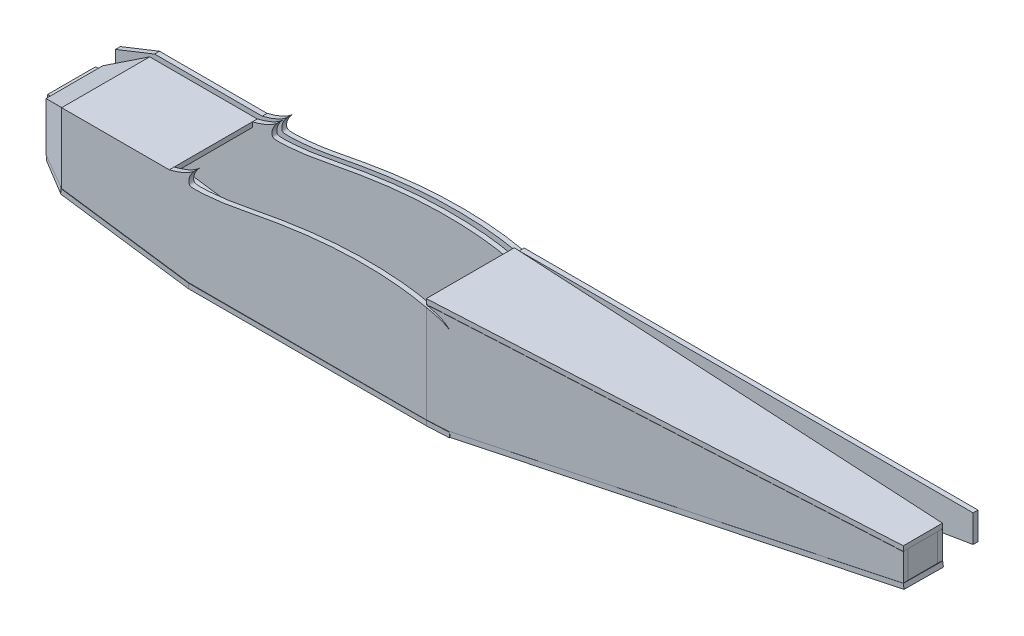
SolidWorks part; units mm, degrees
material "Default"
ref_plane "Front Plane" through (0, 0, 0) normal (0, 0, 1) x (1, 0, 0)
ref_plane "Top Plane" through (0, 0, 0) normal (0, 1, 0) x (1, 0, 0)
ref_plane "Right Plane" through (0, 0, 0) normal (1, 0, 0) x (0, 0, -1)
other "Center of Mass"
curve "Curve1"
  spline degree 3 poles (264.9706, 0.6908, 0) (266.2411, -0.1717, 0) (265.1272, 0.6583, 0) (264.3876, 1.3839, 0) (262.7456, 2.8995, 0) (260.8083, 4.5118, 0) (258.1583, 6.1371, 0) (254.863, 7.7123, 0) (250.8848, 9.3562, 0) (246.2298, 11.0459, 0) (240.9197, 12.7694, 0) (234.982, 14.5119, 0) (228.45, 16.2652, 0) (221.3598, 18.0131, 0) (213.752, 19.7429, 0) (205.6719, 21.444, 0) (197.169, 23.1075, 0) (188.2928, 24.713, 0) (179.0993, 26.2581, 0) (169.6415, 27.723, 0) (159.9806, 29.1106, 0) (150.1784, 30.4098, 0) (140.3059, 31.6165, 0) (130.4421, 32.7392, 0) (120.6687, 33.7497, 0) (111.0652, 34.6289, 0) (101.6992, 35.3274, 0) (92.6242, 35.8079, 0) (83.8906, 36.0154, 0) (75.5433, 35.9933, 0) (67.5978, 35.5846, 0) (60.0511, 34.7564, 0) (52.8723, 33.5853, 0) (46.0598, 32.0681, 0) (39.6205, 30.289, 0) (33.5818, 28.2794, 0) (27.9692, 26.0865, 0) (22.8177, 23.7219, 0) (18.1438, 21.2336, 0) (13.9729, 18.6499, 0) (10.3312, 16.0059, 0) (7.2202, 13.3576, 0) (4.6849, 10.676, 0) (2.7376, 7.9845, 0) (1.2991, 5.366, 0) (0.3772, 2.8798, 0) (-0.0621, 0.5851, 0) (0.0227, -1.3557, 0) (0.5223, -3.1357, 0) (2.3797, -4.0193, 0) (4.8769, -4.1433, 0) (8.293, -4.2635, 0) (12.5891, -4.0782, 0) (17.7166, -3.7378, 0) (23.6183, -3.1924, 0) (30.2339, -2.4546, 0) (37.5312, -1.5084, 0) (45.5065, -0.186, 0) (54.1987, 1.4724, 0) (63.6513, 3.2771, 0) (73.8181, 5.1827, 0) (84.6351, 7.11, 0) (96.023, 8.9867, 0) (107.8934, 10.7501, 0) (120.1441, 12.3356, 0) (132.6647, 13.6969, 0) (145.3372, 14.7729, 0) (158.0342, 15.5357, 0) (170.6232, 15.9551, 0) (182.9675, 16.008, 0) (194.9296, 15.691, 0) (206.3723, 15.0115, 0) (217.1581, 13.9781, 0) (227.1585, 12.6306, 0) (236.2435, 11.0081, 0) (244.3064, 9.1649, 0) (251.1986, 7.1926, 0) (256.8393, 5.0876, 0) (260.8637, 3.1612, 0) (263.8308, 1.3801, 0) (264.9706, 0.6908, 0) (266.2411, -0.1717, 0) (265.1272, 0.6583, 0) knots -0.009748 -0.004147 -0.001 0 0.00098 0.003649 0.007483 0.012095 0.017526 0.024052 0.031783 0.040678 0.05071 0.061833 0.073989 0.087118 0.101145 0.115991 0.13157 0.147788 0.164551 0.181758 0.199312 0.217095 0.23499 0.252857 0.270541 0.287887 0.304773 0.321101 0.336806 0.3518 0.366031 0.379616 0.392653 0.40517 0.417172 0.428604 0.439419 0.449597 0.459102 0.467908 0.475988 0.483309 0.489875 0.495803 0.501149 0.505903 0.510047 0.513579 0.516447 0.51935 0.523823 0.529974 0.537716 0.546968 0.557637 0.56962 0.582804 0.597247 0.613135 0.630444 0.649056 0.668822 0.689595 0.71119 0.733427 0.756094 0.778989 0.80189 0.824567 0.846792 0.868338 0.888978 0.908492 0.926659 0.943286 0.958169 0.971136 0.981956 0.990252 0.995853 0.999 1 1.00098 1.003649 1.007483 periodic
sketch "Sketch2" plane through (0, 0, 0) normal (0, 0, 1) x (1, 0, 0)
  line L0 (242.745, 12.1672) -> (706.745, 12.1672)
  line L1 (706.745, 12.1672) -> (706.745, -15.8895)
  line L3 (0, 0) -> (-0.0046, 0)
  line L4 (-130, 0) -> (-20, 0)
  line L5 (-20, 0) -> (-130, 0)
  line L6 (124.4328, 12.1672) -> (124.4328, 12.7877)
  line L7 (-0.0046, 0) -> (-0.0046, -0.1771)
  line L8 (265.9954, -90) -> (706.745, -15.8895)
  line L13 (124.4328, 12.1672) -> (119.0969, 12.1672) construction
  line L14 (-0.0046, -90) -> (265.9954, -90)
  line L16 (-170, -15.8895) -> (-170, -65.8895) construction
  line L17 (-130, 0) -> (-170, -15.8895)
  line L18 (-170, -15.8895) -> (-170, -65.8895)
  line L19 (-170, -65.8895) -> (-0.0046, -90)
  spline S0 degree 3 poles (264.9706, 0.6908) (266.2411, -0.1717) (265.1272, 0.6583) (264.3876, 1.3839) (262.7456, 2.8995) (260.8083, 4.5118) (258.1583, 6.1371) (254.863, 7.7123) (250.8848, 9.3562) (246.2298, 11.0459) (240.9197, 12.7694) (234.982, 14.5119) (228.45, 16.2652) (221.3598, 18.0131) (213.752, 19.7429) (205.6719, 21.444) (197.169, 23.1075) (188.2928, 24.713) (179.0993, 26.2581) (169.6415, 27.723) (159.9806, 29.1106) (150.1784, 30.4098) (140.3059, 31.6165) (130.4421, 32.7392) (120.6687, 33.7497) (111.0652, 34.6289) (101.6992, 35.3274) (92.6242, 35.8079) (83.8906, 36.0154) (75.5433, 35.9933) (67.5978, 35.5846) (60.0511, 34.7564) (52.8723, 33.5853) (46.0598, 32.0681) (39.6205, 30.289) (33.5818, 28.2794) (27.9692, 26.0865) (22.8177, 23.7219) (18.1438, 21.2336) (13.9729, 18.6499) (10.3312, 16.0059) (7.2202, 13.3576) (4.6849, 10.676) (2.7376, 7.9845) (1.2991, 5.366) (0.3772, 2.8798) (-0.0621, 0.5851) (0.0227, -1.3557) (0.5223, -3.1357) (2.3797, -4.0193) (4.8769, -4.1433) (8.293, -4.2635) (12.5891, -4.0782) (17.7166, -3.7378) (23.6183, -3.1924) (30.2339, -2.4546) (37.5312, -1.5084) (45.5065, -0.186) (54.1987, 1.4724) (63.6513, 3.2771) (73.8181, 5.1827) (84.6351, 7.11) (96.023, 8.9867) (107.8934, 10.7501) (120.1441, 12.3356) (132.6647, 13.6969) (145.3372, 14.7729) (158.0342, 15.5357) (170.6232, 15.9551) (182.9675, 16.008) (194.9296, 15.691) (206.3723, 15.0115) (217.1581, 13.9781) (227.1585, 12.6306) (236.2435, 11.0081) (244.3064, 9.1649) (251.1986, 7.1926) (256.8393, 5.0876) (260.8637, 3.1612) (263.8308, 1.3801) (264.9706, 0.6908) (266.2411, -0.1717) (265.1272, 0.6583) knots -0.009748 -0.004147 -0.001 0 0.00098 0.003649 0.007483 0.012095 0.017526 0.024052 0.031783 0.040678 0.05071 0.061833 0.073989 0.087118 0.101145 0.115991 0.13157 0.147788 0.164551 0.181758 0.199312 0.217095 0.23499 0.252857 0.270541 0.287887 0.304773 0.321101 0.336806 0.3518 0.366031 0.379616 0.392653 0.40517 0.417172 0.428604 0.439419 0.449597 0.459102 0.467908 0.475988 0.483309 0.489875 0.495803 0.501149 0.505903 0.510047 0.513579 0.516447 0.51935 0.523823 0.529974 0.537716 0.546968 0.557637 0.56962 0.582804 0.597247 0.613135 0.630444 0.649056 0.668822 0.689595 0.71119 0.733427 0.756094 0.778989 0.80189 0.824567 0.846792 0.868338 0.888978 0.908492 0.926659 0.943286 0.958169 0.971136 0.981956 0.990252 0.995853 0.999 1 1.00098 1.003649 1.007483 only from (266, 0) to (266, 0) construction
  spline S1 degree 3 poles (7.0158, 13.0653) (6.1882, 12.2656) (4.6442, 10.6197) (2.7376, 7.9845) (1.2991, 5.366) (0.3772, 2.8798) (-0.0621, 0.5851) (0.0227, -1.3557) (0.5223, -3.1357) (2.3797, -4.0193) (4.8769, -4.1433) (8.293, -4.2635) (12.5891, -4.0782) (17.7166, -3.7378) (23.6183, -3.1924) (30.2339, -2.4546) (37.5312, -1.5084) (45.5065, -0.186) (54.1987, 1.4724) (63.6513, 3.2771) (73.8181, 5.1827) (84.6351, 7.11) (96.023, 8.9867) (107.8934, 10.7501) (120.1441, 12.3356) (132.6647, 13.6969) (145.3372, 14.7729) (158.0342, 15.5357) (170.6232, 15.9551) (182.9675, 16.008) (194.9296, 15.691) (206.3723, 15.0115) (217.1581, 13.9781) (227.1585, 12.6306) (236.2435, 11.0081) (244.3064, 9.1649) (251.1986, 7.1926) (256.8393, 5.0876) (260.8637, 3.1612) (263.8308, 1.3801) (264.9706, 0.6908) (266.2411, -0.1717) (265.1272, 0.6583) (264.3876, 1.3839) (262.7456, 2.8995) (260.8083, 4.5118) (258.1583, 6.1371) (254.863, 7.7123) (250.8848, 9.3562) (246.7685, 10.8503) (243.9744, 11.7746) (242.745, 12.1672) knots 0.483683 0.483683 0.483683 0.483683 0.489875 0.495803 0.501149 0.505903 0.510047 0.513579 0.516447 0.51935 0.523823 0.529974 0.537716 0.546968 0.557637 0.56962 0.582804 0.597247 0.613135 0.630444 0.649056 0.668822 0.689595 0.71119 0.733427 0.756094 0.778989 0.80189 0.824567 0.846792 0.868338 0.888978 0.908492 0.926659 0.943286 0.958169 0.971136 0.981956 0.990252 0.995853 0.999 1 1.00098 1.003649 1.007483 1.012095 1.017526 1.024052 1.031783 1.040678 1.047625 1.047625 1.047625 1.047625
  spline S2 degree 3 poles (-20, 0) (-11.0921, 2.2966) (0.1137, 5.807) (7.0158, 13.0653) knots 0 0 0 0 0.787091 0.787091 0.787091 0.787091
  dimension "D1" = 464
  dimension "D2" = 130
  dimension "D5" = 28.0567
extrude "Boss-Extrude1" add sketch "Sketch2" along normal blind 5
ref_plane "Plane2" through (0, 0, 100) normal (0, 0, 1) x (1, 0, 0)
sketch "Sketch7" plane through (0, 0, 100) normal (0, 0, 1) x (1, 0, 0)
  line L0 (242.745, 12.1672) -> (242.745, -90)
  line L1 (242.745, -90) -> (265.9954, -90)
  line L2 (-130, 0) -> (-130, -71.5627)
  line L3 (242.745, 9.4844) -> (242.745, 8.9727)
  line L4 (-130, 0) -> (-130, -71.5627)
  line L5 (242.745, 8.9727) -> (242.745, 9.4844)
  line L6 (-130, 0) -> (-130, -71.5627)
  line L7 (242.745, 9.4844) -> (242.745, -90)
  line L8 (-20, 0) -> (-130, 0)
  line L9 (-130, 0) -> (-170, -15.8895)
  line L10 (-170, -15.8895) -> (-170, -65.8895)
  line L11 (-170, -65.8895) -> (-0.0046, -90)
  line L12 (-0.0046, -90) -> (265.9954, -90)
  line L13 (265.9954, -90) -> (706.745, -15.8895)
  line L14 (706.745, -15.8895) -> (706.745, 12.1672)
  line L15 (706.745, 12.1672) -> (242.745, 12.1672)
  line L16 (-20, 0) -> (-130, 0)
  line L17 (-130, 0) -> (-170, -15.8895)
  line L18 (-170, -15.8895) -> (-170, -65.8895)
  line L19 (-170, -65.8895) -> (-0.0046, -90)
  line L20 (-0.0046, -90) -> (265.9954, -90)
  line L21 (265.9954, -90) -> (706.745, -15.8895)
  line L22 (706.745, -15.8895) -> (706.745, 12.1672)
  line L23 (706.745, 12.1672) -> (242.745, 12.1672)
  spline S0 degree 3 poles (242.745, 9.4844) (240.69, 9.9881) (235.6053, 11.1221) (227.1585, 12.6306) (217.1581, 13.9781) (206.3723, 15.0115) (194.9296, 15.691) (182.9675, 16.008) (170.6232, 15.9551) (158.0342, 15.5357) (145.3372, 14.7729) (132.6647, 13.6969) (120.1441, 12.3356) (107.8934, 10.7501) (96.023, 8.9867) (84.6351, 7.11) (73.8181, 5.1827) (63.6513, 3.2771) (54.1987, 1.4724) (45.5065, -0.186) (37.5312, -1.5084) (30.2339, -2.4546) (23.6183, -3.1924) (17.7166, -3.7378) (12.5891, -4.0782) (8.293, -4.2635) (4.8769, -4.1433) (2.3797, -4.0193) (0.5223, -3.1357) (0.0227, -1.3557) (-0.0621, 0.5851) (0.3772, 2.8798) (1.2991, 5.366) (2.7376, 7.9845) (4.3959, 10.2766) (5.6165, 11.6415) (6.1205, 12.1672) knots 0.578902 0.578902 0.578902 0.578902 0.590296 0.606923 0.62509 0.644604 0.665244 0.68679 0.709016 0.731692 0.754594 0.777488 0.800155 0.822393 0.843987 0.86476 0.884526 0.903139 0.920447 0.936335 0.950778 0.963962 0.975945 0.986614 0.995867 1.003608 1.009759 1.014232 1.017135 1.020003 1.023535 1.027679 1.032433 1.037779 1.043708 1.047625 1.047625 1.047625 1.047625
  spline S2 degree 3 poles (2011.2676, 4666.7582) (-142.2329, -124.2279) (96.248, 65.4868) (250.8848, 9.3562) (254.863, 7.7123) (258.1583, 6.1371) (260.8083, 4.5118) (262.7456, 2.8995) (264.3876, 1.3839) (265.1272, 0.6583) (266.2411, -0.1717) (264.9706, 0.6908) (263.8308, 1.3801) (260.8637, 3.1612) (256.8393, 5.0876) (251.1986, 7.1926) (244.3064, 9.1649) (236.2435, 11.0081) (227.1585, 12.6306) (217.1581, 13.9781) (206.3723, 15.0115) (194.9296, 15.691) (182.9675, 16.008) (170.6232, 15.9551) (158.0342, 15.5357) (145.3372, 14.7729) (132.6647, 13.6969) (120.1441, 12.3356) (107.8934, 10.7501) (96.023, 8.9867) (84.6351, 7.11) (73.8181, 5.1827) (63.6513, 3.2771) (54.1987, 1.4724) (45.5065, -0.186) (37.5312, -1.5084) (30.2339, -2.4546) (23.6183, -3.1924) (17.7166, -3.7378) (12.5891, -4.0782) (8.293, -4.2635) (4.8769, -4.1433) (2.3797, -4.0193) (0.5223, -3.1357) (0.0227, -1.3557) (-0.0621, 0.5851) (0.3772, 2.8798) (1.2991, 5.366) (2.7376, 7.9845) (49.3907, 72.4654) (363.3472, -85.3871) (-4760.2536, 1520.3218) knots -0.376049 -0.376049 -0.376049 -0.376049 0.492904 0.501799 0.50953 0.516057 0.521487 0.526099 0.529933 0.532602 0.533582 0.534582 0.53773 0.54333 0.551627 0.562446 0.575413 0.590296 0.606923 0.62509 0.644604 0.665244 0.68679 0.709016 0.731692 0.754594 0.777488 0.800155 0.822393 0.843987 0.86476 0.884526 0.903139 0.920447 0.936335 0.950778 0.963962 0.975945 0.986614 0.995867 1.003608 1.009759 1.014232 1.017135 1.020003 1.023535 1.027679 1.032433 1.037779 1.043708 1.459832 1.459832 1.459832 1.459832 only from (242.745, 12.1672) to (6.1205, 12.1672)
  spline S3 degree 3 poles (-2585.8794, 1507.7799) (2947.8526, -1206.4866) (-3071.6527, 1002.673) (2847.1057, -882.3761) knots -5.429819 -5.429819 -5.429819 -5.429819 6.58664 6.58664 6.58664 6.58664 only from (6.1205, 12.1672) to (-20, 0)
  spline S4 degree 3 poles (242.745, 12.1672) (243.9744, 11.7746) (246.7685, 10.8503) (250.8848, 9.3562) (254.863, 7.7123) (258.1583, 6.1371) (260.8083, 4.5118) (262.7456, 2.8995) (264.3876, 1.3839) (265.1272, 0.6583) (266.2411, -0.1717) (264.9706, 0.6908) (263.8308, 1.3801) (260.8637, 3.1612) (256.8393, 5.0876) (251.1986, 7.1926) (246.3371, 8.5838) (243.3744, 9.3301) (242.745, 9.4844) knots 0.485957 0.485957 0.485957 0.485957 0.492904 0.501799 0.50953 0.516057 0.521487 0.526099 0.529933 0.532602 0.533582 0.534582 0.53773 0.54333 0.551627 0.562446 0.575413 0.578902 0.578902 0.578902 0.578902
  spline S5 degree 3 poles (6.1205, 12.1672) (-0.8269, 5.5132) (-11.4676, 2.1998) (-20, 0) knots 0 0 0 0 0.753912 0.753912 0.753912 0.753912
  dimension "D2" = 50
  dimension "D1" = 0
ref_plane "Plane3" through (6.088, 0, 112.7755) normal (0.0539, 0, 0.9985) x (0, -1, 0)
sketch "Sketch9" plane through (6.088, 0, 112.7755) normal (0.0539, 0, 0.9985) x (0, -1, 0)
sketch "Sketch12" plane through (6.088, 0, 112.7755) normal (0.0539, 0, 0.9985) x (0, -1, 0)
  line L0 (15.8895, 700.327) -> (-12.1672, 700.327) construction
  line L1 (90, 260.2182) -> (15.8895, 700.327) construction
  line L2 (90, 237.0016) -> (90, 260.2182) construction
  line L3 (-12.1672, 700.327) -> (-12.1672, 237.0016) construction
  line L4 (15.8895, 700.327) -> (-12.1672, 700.327)
  line L5 (90, 260.2182) -> (15.8895, 700.327)
  line L6 (90, 237.0016) -> (90, 260.2182)
  line L7 (-12.1672, 700.327) -> (-12.1672, 237.0016)
  line L8 (-9.5488, 236.7508) -> (-9.4844, 237.0016)
  line L9 (-9.4844, 237.0016) -> (90, 237.0016)
  spline S0 degree 3 poles (-1920.9953, 797.0816) (45.2116, -34.5204) (-51.6861, 128.6823) (-9.3562, 245.1296) (-7.7123, 249.102) (-6.1371, 252.3925) (-4.5118, 255.0387) (-2.8995, 256.9731) (-1.3839, 258.6128) (-0.6583, 259.3512) (0.1717, 260.4636) (-0.6908, 259.1949) (-1.3801, 258.0568) (-3.1612, 255.094) (-5.0876, 251.0754) (-7.1926, 245.443) (-48.2208, 102.2773) (127.5498, -107.7619) (-1558.7508, 1492.8674) knots -0.158315 -0.158315 -0.158315 -0.158315 0.492904 0.501799 0.50953 0.516057 0.521487 0.526099 0.529933 0.532602 0.533582 0.534582 0.53773 0.54333 0.551627 0.562446 0.575413 1.356035 1.356035 1.356035 1.356035 only from (-12.1672, 237.0016) to (-9.4844, 237.0016) construction
  spline S1 degree 3 poles (-12.1672, 237.0016) (-11.7746, 238.2292) (-10.8503, 241.0193) (-9.3562, 245.1296) (-7.7123, 249.102) (-6.1371, 252.3925) (-4.5118, 255.0387) (-2.8995, 256.9731) (-1.3839, 258.6128) (-0.6583, 259.3512) (0.1717, 260.4636) (-0.6908, 259.1949) (-1.3801, 258.0568) (-3.1612, 255.094) (-5.0876, 251.0754) (-7.1926, 245.443) (-8.5838, 240.5885) (-9.3301, 237.6301) (-9.4844, 237.0016) knots 0.485957 0.485957 0.485957 0.485957 0.492904 0.501799 0.50953 0.516057 0.521487 0.526099 0.529933 0.532602 0.533582 0.534582 0.53773 0.54333 0.551627 0.562446 0.575413 0.578902 0.578902 0.578902 0.578902
sketch "Sketch14" plane through (6.088, 0, 112.7755) normal (0.0539, 0, 0.9985) x (0, -1, 0)
  line L0 (-9.4844, 237.0016) -> (90, 237.0016)
sketch "Sketch19" plane through (6.088, 0, 112.7755) normal (0.0539, 0, 0.9985) x (0, -1, 0)
extrude "Boss-Extrude5" add sketch "Sketch12" against normal blind 5 separate body contours L7 S1 L9 L6 L5 L4
ref_plane "Plane4" through (-65.9855, 0, 132.0002) normal (-0.4471, 0, 0.8945) x (0, -1, 0)
sketch "Sketch22" plane through (0, 0, 100) normal (0, 0, 1) x (1, 0, 0)
  line L0 (-130, -71.5627) -> (-170, -65.8895)
sketch "Sketch23" plane through (0, 0, 100) normal (0, 0, 1) x (1, 0, 0)
  line L0 (-130, -71.5627) -> (-170, -65.8895) construction
  line L1 (-130, 0) -> (-130, -71.5627) construction
  line L2 (-170, -15.8895) -> (-170, -65.8895) construction
  line L3 (-130, 0) -> (-170, -15.8895) construction
  line L4 (-130, -71.5627) -> (-170, -65.8895)
  line L5 (-130, 0) -> (-130, -71.5627)
  line L6 (-170, -15.8895) -> (-170, -65.8895)
  line L7 (-130, 0) -> (-170, -15.8895)
sketch "Sketch24" plane through (-65.9855, 0, 132.0002) normal (-0.4471, 0, 0.8945) x (0, -1, 0)
  line L0 (0, -71.5672) -> (71.5627, -71.5672) construction
  line L1 (15.8895, -107.3459) -> (65.8895, -107.3459) construction
  line L2 (0, -71.5672) -> (15.8895, -107.3459) construction
  line L3 (0, -71.5672) -> (71.5627, -71.5672)
  line L4 (65.8895, -107.3459) -> (71.5627, -71.5672)
  line L5 (15.8895, -107.3459) -> (65.8895, -107.3459)
  line L6 (0, -71.5672) -> (15.8895, -107.3459)
  line L7 (71.5627, -71.5672) -> (0, -71.5672)
  line L8 (65.8895, -107.3459) -> (71.5627, -71.5672)
  line L9 (15.8895, -107.3459) -> (65.8895, -107.3459)
  line L10 (0, -71.5672) -> (15.8895, -107.3459)
  line L11 (71.5627, -71.5672) -> (0, -71.5672)
  line L12 (15.8895, -107.3459) -> (65.8895, -107.3459)
  line L13 (0, -71.5672) -> (15.8895, -107.3459)
  dimension "D1" = 0
extrude "Boss-Extrude7" add sketch "Sketch24" against normal blind 5 separate body contours L3 L10 L9 L8
sketch "Sketch26" plane through (0, 0, 100) normal (0, 0, 1) x (1, 0, 0)
extrude "Boss-Extrude8" add sketch "Sketch7" against normal blind 5 and the other way blind 0.0024 separate body
sketch "Sketch27" plane through (0, 0, 100) normal (0, 0, 1) x (1, 0, 0)
  spline S0 degree 3 poles (264.9706, 0.6908) (266.2411, -0.1717) (265.1272, 0.6583) (264.3876, 1.3839) (262.7456, 2.8995) (260.8083, 4.5118) (258.1583, 6.1371) (254.863, 7.7123) (250.8848, 9.3562) (246.2298, 11.0459) (240.9197, 12.7694) (234.982, 14.5119) (228.45, 16.2652) (221.3598, 18.0131) (213.752, 19.7429) (205.6719, 21.444) (197.169, 23.1075) (188.2928, 24.713) (179.0993, 26.2581) (169.6415, 27.723) (159.9806, 29.1106) (150.1784, 30.4098) (140.3059, 31.6165) (130.4421, 32.7392) (120.6687, 33.7497) (111.0652, 34.6289) (101.6992, 35.3274) (92.6242, 35.8079) (83.8906, 36.0154) (75.5433, 35.9933) (67.5978, 35.5846) (60.0511, 34.7564) (52.8723, 33.5853) (46.0598, 32.0681) (39.6205, 30.289) (33.5818, 28.2794) (27.9692, 26.0865) (22.8177, 23.7219) (18.1438, 21.2336) (13.9729, 18.6499) (10.3312, 16.0059) (7.2202, 13.3576) (4.6849, 10.676) (2.7376, 7.9845) (1.2991, 5.366) (0.3772, 2.8798) (-0.0621, 0.5851) (0.0227, -1.3557) (0.5223, -3.1357) (2.3797, -4.0193) (4.8769, -4.1433) (8.293, -4.2635) (12.5891, -4.0782) (17.7166, -3.7378) (23.6183, -3.1924) (30.2339, -2.4546) (37.5312, -1.5084) (45.5065, -0.186) (54.1987, 1.4724) (63.6513, 3.2771) (73.8181, 5.1827) (84.6351, 7.11) (96.023, 8.9867) (107.8934, 10.7501) (120.1441, 12.3356) (132.6647, 13.6969) (145.3372, 14.7729) (158.0342, 15.5357) (170.6232, 15.9551) (182.9675, 16.008) (194.9296, 15.691) (206.3723, 15.0115) (217.1581, 13.9781) (227.1585, 12.6306) (236.2435, 11.0081) (244.3064, 9.1649) (251.1986, 7.1926) (256.8393, 5.0876) (260.8637, 3.1612) (263.8308, 1.3801) (264.9706, 0.6908) (266.2411, -0.1717) (265.1272, 0.6583) knots -0.009748 -0.004147 -0.001 0 0.00098 0.003649 0.007483 0.012095 0.017526 0.024052 0.031783 0.040678 0.05071 0.061833 0.073989 0.087118 0.101145 0.115991 0.13157 0.147788 0.164551 0.181758 0.199312 0.217095 0.23499 0.252857 0.270541 0.287887 0.304773 0.321101 0.336806 0.3518 0.366031 0.379616 0.392653 0.40517 0.417172 0.428604 0.439419 0.449597 0.459102 0.467908 0.475988 0.483309 0.489875 0.495803 0.501149 0.505903 0.510047 0.513579 0.516447 0.51935 0.523823 0.529974 0.537716 0.546968 0.557637 0.56962 0.582804 0.597247 0.613135 0.630444 0.649056 0.668822 0.689595 0.71119 0.733427 0.756094 0.778989 0.80189 0.824567 0.846792 0.868338 0.888978 0.908492 0.926659 0.943286 0.958169 0.971136 0.981956 0.990252 0.995853 0.999 1 1.00098 1.003649 1.007483 only from (266, 0) to (266, 0) construction
  spline S1 degree 3 poles (264.9706, 0.6908) (266.2411, -0.1717) (265.1272, 0.6583) (264.3876, 1.3839) (262.7456, 2.8995) (260.8083, 4.5118) (258.1583, 6.1371) (254.863, 7.7123) (250.8848, 9.3562) (246.2298, 11.0459) (240.9197, 12.7694) (234.982, 14.5119) (228.45, 16.2652) (221.3598, 18.0131) (213.752, 19.7429) (205.6719, 21.444) (197.169, 23.1075) (188.2928, 24.713) (179.0993, 26.2581) (169.6415, 27.723) (159.9806, 29.1106) (150.1784, 30.4098) (140.3059, 31.6165) (130.4421, 32.7392) (120.6687, 33.7497) (111.0652, 34.6289) (101.6992, 35.3274) (92.6242, 35.8079) (83.8906, 36.0154) (75.5433, 35.9933) (67.5978, 35.5846) (60.0511, 34.7564) (52.8723, 33.5853) (46.0598, 32.0681) (39.6205, 30.289) (33.5818, 28.2794) (27.9692, 26.0865) (22.8177, 23.7219) (18.1438, 21.2336) (13.9729, 18.6499) (10.3312, 16.0059) (7.2202, 13.3576) (4.6849, 10.676) (2.7376, 7.9845) (1.2991, 5.366) (0.3772, 2.8798) (-0.0621, 0.5851) (0.0227, -1.3557) (0.5223, -3.1357) (2.3797, -4.0193) (4.8769, -4.1433) (8.293, -4.2635) (12.5891, -4.0782) (17.7166, -3.7378) (23.6183, -3.1924) (30.2339, -2.4546) (37.5312, -1.5084) (45.5065, -0.186) (54.1987, 1.4724) (63.6513, 3.2771) (73.8181, 5.1827) (84.6351, 7.11) (96.023, 8.9867) (107.8934, 10.7501) (120.1441, 12.3356) (132.6647, 13.6969) (145.3372, 14.7729) (158.0342, 15.5357) (170.6232, 15.9551) (182.9675, 16.008) (194.9296, 15.691) (206.3723, 15.0115) (217.1581, 13.9781) (227.1585, 12.6306) (236.2435, 11.0081) (244.3064, 9.1649) (251.1986, 7.1926) (256.8393, 5.0876) (260.8637, 3.1612) (263.8308, 1.3801) (264.9706, 0.6908) (266.2411, -0.1717) (265.1272, 0.6583) knots -0.009748 -0.004147 -0.001 0 0.00098 0.003649 0.007483 0.012095 0.017526 0.024052 0.031783 0.040678 0.05071 0.061833 0.073989 0.087118 0.101145 0.115991 0.13157 0.147788 0.164551 0.181758 0.199312 0.217095 0.23499 0.252857 0.270541 0.287887 0.304773 0.321101 0.336806 0.3518 0.366031 0.379616 0.392653 0.40517 0.417172 0.428604 0.439419 0.449597 0.459102 0.467908 0.475988 0.483309 0.489875 0.495803 0.501149 0.505903 0.510047 0.513579 0.516447 0.51935 0.523823 0.529974 0.537716 0.546968 0.557637 0.56962 0.582804 0.597247 0.613135 0.630444 0.649056 0.668822 0.689595 0.71119 0.733427 0.756094 0.778989 0.80189 0.824567 0.846792 0.868338 0.888978 0.908492 0.926659 0.943286 0.958169 0.971136 0.981956 0.990252 0.995853 0.999 1 1.00098 1.003649 1.007483 only from (266, 0) to (266, 0)
ref_plane "Plane5" through (0, 0, 55) normal (0, 0, 1) x (1, 0, 0)
mirror "Mirror8" about plane through (0, 0, 55) normal (0, 0, 1) of bodies 110 107 109
ref_plane "Plane11" through (-159.7671, 0, 0) normal (-1, 0, 0) x (0, 0, 1)
sketch "Sketch29" plane through (-159.7671, 0, 0) normal (-1, 0, 0) x (0, 0, 1)
  line L0 (30.4702, -15.8895) -> (79.5298, -15.8895)
  line L1 (79.5298, -65.8895) -> (30.4702, -65.8895)
  line L2 (30.4702, -15.8895) -> (30.4702, -65.8895)
  line L3 (79.5298, -15.8895) -> (79.5298, -65.8895)
extrude "Boss-Extrude9" add sketch "Sketch29" along normal blind 5 separate body
ref_plane "Plane12" through (705.1272, 0, 0) normal (-1, 0, 0) x (0, 0, 1)
sketch "Sketch30" plane through (705.1272, 0, 0) normal (-1, 0, 0) x (0, 0, 1)
  line L0 (70.0319, 12.1672) -> (39.9681, 12.1672)
  line L1 (39.9681, 12.1672) -> (39.9681, -15.8895)
  line L2 (39.9681, -15.8895) -> (70.0319, -15.8895)
  line L3 (70.0319, -15.8895) -> (70.0319, 12.1672)
extrude "Boss-Extrude10" add sketch "Sketch30" along normal blind 5 separate body
ref_plane "Plane13" through (-25.7093, 51.7807, 0) normal (0.4447, -0.8957, 0) x (-0.8957, -0.4447, 0)
sketch "Sketch31" plane through (-25.7093, 51.7807, 0) normal (0.4447, -0.8957, 0) x (-0.8957, -0.4447, 0)
  line L0 (116.4379, -9.9976) -> (116.4379, -99.8186)
  line L2 (116.4379, -100.0024) -> (116.4379, -95) construction
  line L3 (116.4379, -99.8186) -> (152.1683, -84.0021)
  line L4 (152.1683, -84.0021) -> (152.1683, -25.9979)
  line L5 (152.1683, -25.9979) -> (116.4379, -9.9976)
extrude "Boss-Extrude11" add sketch "Sketch31" along normal blind 5
ref_plane "Plane14" through (0, 0, 0) normal (0, 1, 0) x (1, 0, 0)
sketch "Sketch32" plane through (0, 0, 0) normal (0, 1, 0) x (1, 0, 0)
  line L0 (-20, -9.9976) -> (-130, -9.9976)
  line L1 (-130, -9.9976) -> (-130, -100)
  line L2 (-130, -100) -> (-20, -100.0024)
  line L3 (-20, -100.0024) -> (-20, -9.9976)
extrude "Boss-Extrude12" add sketch "Sketch32" against normal blind 5
ref_plane "Plane17" through (0, 12.3672, 0) normal (0, 1, 0) x (1, 0, 0)
sketch "Sketch35" plane through (0, 12.3672, 0) normal (0, 1, 0) x (1, 0, 0)
  line L0 (242.745, -100.0024) -> (242.745, -9.9976)
  line L1 (242.745, -9.9976) -> (705.3968, -34.9753)
  line L2 (705.3968, -34.9753) -> (705.3968, -75.0247)
  line L3 (705.3968, -75.0247) -> (242.745, -100.0024)
extrude "Boss-Extrude18" add sketch "Sketch35" along normal blind 5 separate body
ref_plane "Plane21" through (22.0837, -131.3362, 1.1921) normal (0.1658, -0.9861, 0.009) x (-0.9862, -0.1658, 0.0015)
sketch "Sketch37" plane through (22.0837, -131.3362, 1.1921) normal (0.1658, -0.9861, 0.009) x (-0.9862, -0.1658, 0.0015)
  line L0 (-693.0803, -34.7694) -> (-693.0803, -75.0777)
  line L1 (-693.0803, -75.0777) -> (-246.5359, -97.98)
  line L2 (-246.5359, -97.98) -> (-246.5359, -10.4141)
  line L3 (-246.5359, -10.4141) -> (-693.0803, -34.7694)
extrude "Boss-Extrude22" add sketch "Sketch37" along normal blind 5
ref_plane "Plane22" through (-12.5468, -88.4635, 0) normal (-0.1404, -0.9901, 0) x (-0.9901, 0.1404, 0)
sketch "Sketch38" plane through (-12.5468, -88.4635, 0) normal (-0.1404, -0.9901, 0) x (-0.9901, 0.1404, 0)
  line L0 (118.7734, -100.2586) -> (118.7734, -9.5481)
  line L1 (118.7734, -9.5481) -> (-12.9761, -9.5481)
  line L2 (-12.9761, -9.5481) -> (-12.9761, -100.2586)
  line L3 (-12.9761, -100.2586) -> (118.7734, -100.2586)
extrude "Boss-Extrude23" add sketch "Sketch38" along normal blind 5 separate body
ref_plane "Plane24" through (-16.2604, -91.7256, 0) normal (-0.1746, -0.9846, 0) x (-0.9846, 0.1746, 0)
sketch "Sketch42" plane through (-12.5498, -88.4849, 6.2735) normal (-0.1401, -0.9877, 0.07) x (-0.9901, 0.1397, -0.0099)
sketch "Sketch43" plane through (-117.5965, 16.6787, 0) normal (-0.9901, 0.1404, 0) x (0, 0, 1)
  line L0 (9.9367, -89.3489) -> (100.2586, -89.3489)
  line L1 (100.2586, -89.3489) -> (9.5481, -89.3489) construction
  line L2 (100.2586, -89.3489) -> (82.267, -40.3404)
sketch "Sketch44" plane through (-16.2604, -91.7256, 0) normal (-0.1746, -0.9846, 0) x (-0.9846, 0.1746, 0)
  line L0 (115.7481, -10.1158) -> (147.5061, -25.8606)
  line L1 (148.0147, -25.9979) -> (115.5129, -10) construction
  line L2 (147.5061, -25.8606) -> (147.5061, -83.3614)
  line L3 (147.5061, -83.3614) -> (116.1802, -99.7915)
  line L4 (115.7481, -10.1158) -> (116.1802, -99.7915)
extrude "Boss-Extrude24" add sketch "Sketch44" along normal blind 5
ref_plane "Plane25" through (0, -90.24, 0) normal (0, -1, 0) x (-1, 0, 0)
sketch "Sketch45" plane through (0, -90.24, 0) normal (0, -1, 0) x (-1, 0, 0)
  line L0 (0.4014, -100.2586) -> (0.4014, -9.5481)
  line L1 (0.4014, -9.5481) -> (-242.745, -9.9976)
  line L2 (-242.745, -9.9976) -> (-242.745, -100.0024)
  line L3 (-242.745, -100.0024) -> (0.4014, -100.2586)
extrude "Boss-Extrude25" add sketch "Sketch45" along normal blind 5
ref_plane "Plane26" through (0, -90.24, 0) normal (0, -1, 0) x (-1, 0, 0)
sketch "Sketch47" plane through (0, -90.24, 0) normal (0, -1, 0) x (-1, 0, 0)
  line L0 (-242.745, -100.0024) -> (-265.2686, -98.8999)
  line L1 (-242.745, -100.0024) -> (0.0216, -100.2582) construction
  line L2 (-265.2686, -98.8999) -> (-265.2686, -11.4569)
  line L3 (-265.2686, -11.4569) -> (-242.745, -9.9976)
  line L4 (-242.745, -9.9976) -> (-242.745, -100.0024)
extrude "Boss-Extrude26" add sketch "Sketch47" along normal blind 5
